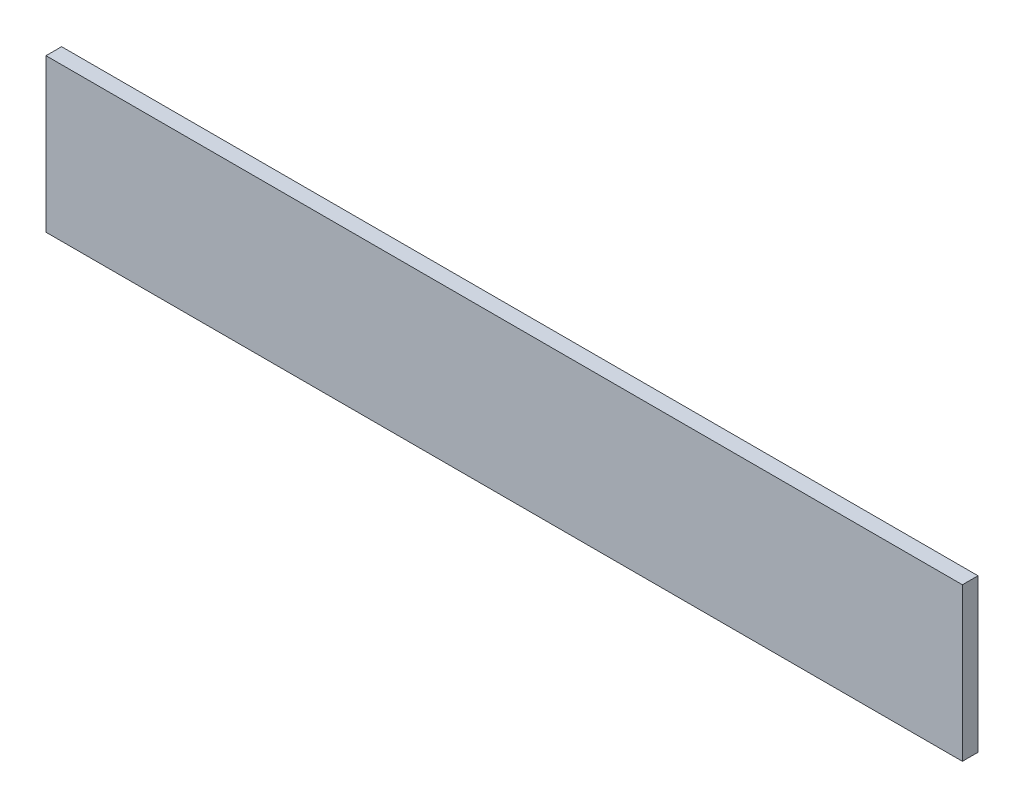
SolidWorks part; units mm, degrees
ref_plane "前视基准面" through (0, 0, 0) normal (0, 0, 1) x (1, 0, 0)
ref_plane "上视基准面" through (0, 0, 0) normal (0, 1, 0) x (1, 0, 0)
ref_plane "右视基准面" through (0, 0, 0) normal (1, 0, 0) x (0, 0, -1)
other "Configuration Table"
sketch "草图1" plane through (0, 0, 0) normal (0, 0, 1) x (1, 0, 0)
  line L1 (-88.03, 14.69) -> (88.03, 14.69)
  line L2 (-88.03, 14.69) -> (-88.03, -14.69)
  line L3 (-88.03, -14.69) -> (88.03, -14.69)
  line L4 (88.03, 14.69) -> (88.03, -14.69)
  line L5 (-88.03, 14.69) -> (88.03, -14.69) construction
  line L6 (-88.03, -14.69) -> (88.03, 14.69) construction
  point P0 (0, 0)
  dimension "D1" = 29.38
  dimension "D2" = 176.06
extrude "凸台-拉伸1" add sketch "草图1" along normal blind 3
